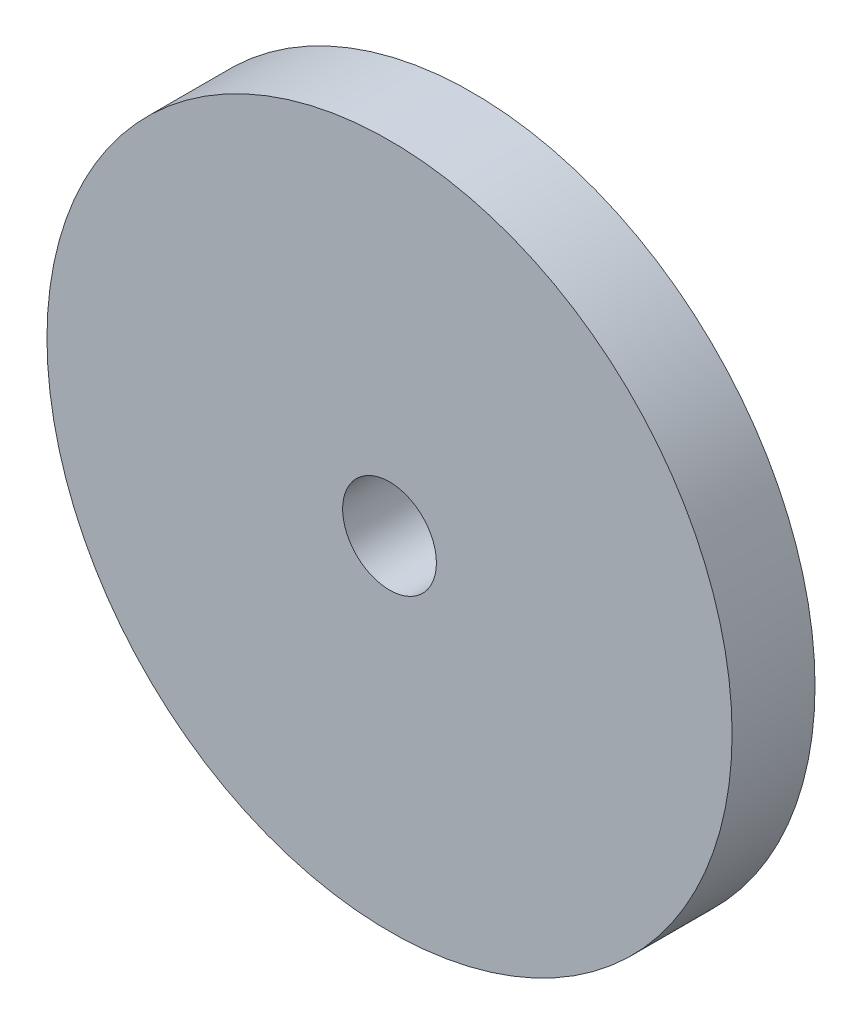
SolidWorks part; units mm, degrees
material "uhlíková ocel 7850"
ref_plane "Přední rovina" through (0, 0, 0) normal (0, 0, 1) x (1, 0, 0)
ref_plane "Horní rovina" through (0, 0, 0) normal (0, 1, 0) x (1, 0, 0)
ref_plane "Pravá rovina" through (0, 0, 0) normal (1, 0, 0) x (0, 0, -1)
sketch "Skica1" plane through (0, 0, 0) normal (0, 0, 1) x (1, 0, 0)
  circle A0 centre (0, 0) radius 9.5
  circle A1 centre (0, 0) radius 1.3
  dimension "D1" = 2.6
  dimension "D2" = 19
extrude "Přidat vysunutím1" add sketch "Skica1" along normal blind 2.3
